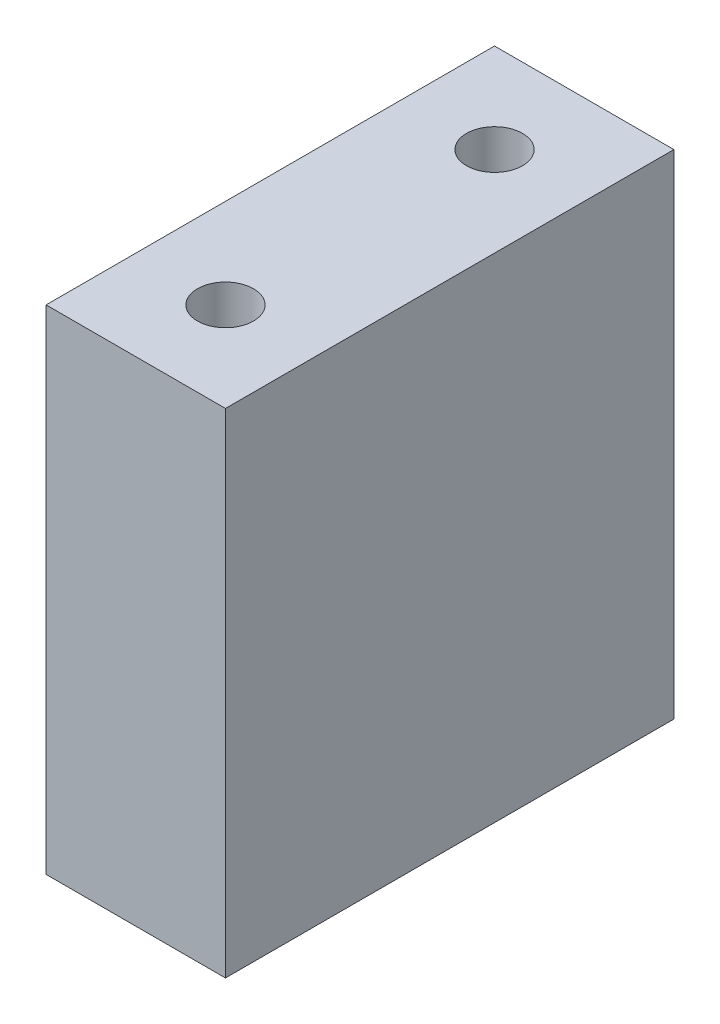
SolidWorks part; units mm, degrees
ref_plane "Front Plane" through (0, 0, 0) normal (0, 0, 1) x (1, 0, 0)
ref_plane "Top Plane" through (0, 0, 0) normal (0, 1, 0) x (1, 0, 0)
ref_plane "Right Plane" through (0, 0, 0) normal (1, 0, 0) x (0, 0, -1)
sketch "Sketch1" plane through (0, 0, 0) normal (1, 0, 0) x (0, 0, -1)
  line L1 (-10, 11) -> (10, 11)
  line L2 (-10, 11) -> (-10, -11)
  line L3 (-10, -11) -> (10, -11)
  line L4 (10, 11) -> (10, -11)
  line L5 (-10, 11) -> (10, -11) construction
  line L6 (-10, -11) -> (10, 11) construction
  point P0 (0, 0)
  dimension "D1" = 20
  dimension "D2" = 22
extrude "Boss-Extrude1" add sketch "Sketch1" along normal mid plane 8
hole_wizard "M3x0.5 Tapped Hole1" positions "Sketch2" profile "Sketch3" tap size "M3x0.5" standard "ANSI Metric"
sketch "Sketch2" plane through (0, 11, 0) normal (0, 1, 0) x (1, 0, 0)
  point P0 (0, 6)
  point P3 (0, -6)
sketch "Sketch3" plane through (0, 11, -6) normal (1, 0, 0) x (0, 0, 1)
  line L0 (0, 0) -> (0, 8.2511)
  line L1 (0, 8.2511) -> (1.25, 7.5)
  line L2 (1.25, 7.5) -> (1.25, 0)
  line L5 (1.25, 0) -> (0, 0)
  line L10 (0, 8.2511) -> (-1.25, 7.5) construction
  line L11 (0, -6.35) -> (0, 107.95) construction
  dimension "Tap Drill Dia." = 2.5
  dimension "Tap Drill Depth" = 7.5
  dimension "Drill Angle" = 118
cosmetic thread "Hole Thread1" parameters "D1"=6, "D2"=3
cosmetic thread "Hole Thread2" parameters "D1"=6, "D2"=3
hole_wizard "M3x0.5 Tapped Hole2" positions "Sketch4" profile "Sketch5" tap size "M3x0.5" standard "ANSI Metric"
sketch "Sketch4" plane through (0, -11, 0) normal (0, -1, 0) x (-1, 0, 0)
  point P0 (0, -6)
  point P3 (0, 6)
sketch "Sketch5" plane through (0, -11, 6) normal (1, 0, 0) x (0, 0, -1)
  line L0 (0, 0) -> (0, 8.2511)
  line L1 (0, 8.2511) -> (1.25, 7.5)
  line L2 (1.25, 7.5) -> (1.25, 0)
  line L5 (1.25, 0) -> (0, 0)
  line L10 (0, 8.2511) -> (-1.25, 7.5) construction
  line L11 (0, -6.35) -> (0, 107.95) construction
  dimension "Tap Drill Dia." = 2.5
  dimension "Tap Drill Depth" = 7.5
  dimension "Drill Angle" = 118
cosmetic thread "Hole Thread3" parameters "D1"=6, "D2"=3
cosmetic thread "Hole Thread4" parameters "D1"=6, "D2"=3
